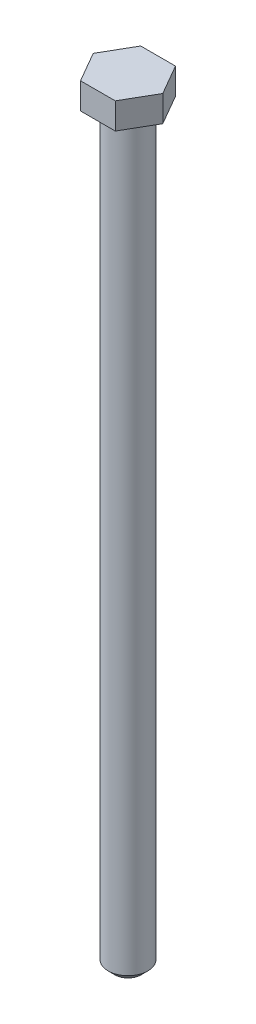
SolidWorks part; units mm, degrees
material "AISI 4130 Steel, annealed at 865C"
ref_plane "Front Plane" through (0, 0, 0) normal (0, 0, 1) x (1, 0, 0)
ref_plane "Top Plane" through (0, 0, 0) normal (0, 1, 0) x (1, 0, 0)
ref_plane "Right Plane" through (0, 0, 0) normal (1, 0, 0) x (0, 0, -1)
sketch "Sketch1" plane through (0, 0, 0) normal (0, 1, 0) x (1, 0, 0)
  line L0 (0, 0) -> (9.6703, 0) construction
  line L1 (8.2636, 0) -> (4.1318, 7.1565)
  line L2 (4.1318, 7.1565) -> (-4.1318, 7.1565)
  line L3 (-4.1318, 7.1565) -> (-8.2636, 0)
  line L4 (-8.2636, 0) -> (-4.1318, -7.1564)
  line L5 (-4.1318, -7.1564) -> (4.1318, -7.1564)
  line L6 (4.1318, -7.1564) -> (8.2636, 0)
  circle A0 centre (0, 0) radius 7.1564 construction
  dimension "D1" = 14.3129
extrude "Extrude1" add sketch "Sketch1" against normal blind 6.223
sketch "Sketch2" plane through (0, -6.223, 0) normal (0, -1, 0) x (1, 0, 0)
  circle A0 centre (0, 0) radius 4.699
  dimension "D1" = 9.398
extrude "Extrude2" add sketch "Sketch2" along normal blind 177.8
chamfer "Chamfer1" distance 1.5875 angle 45 1 edges at (0, -184.023, -4.699)
